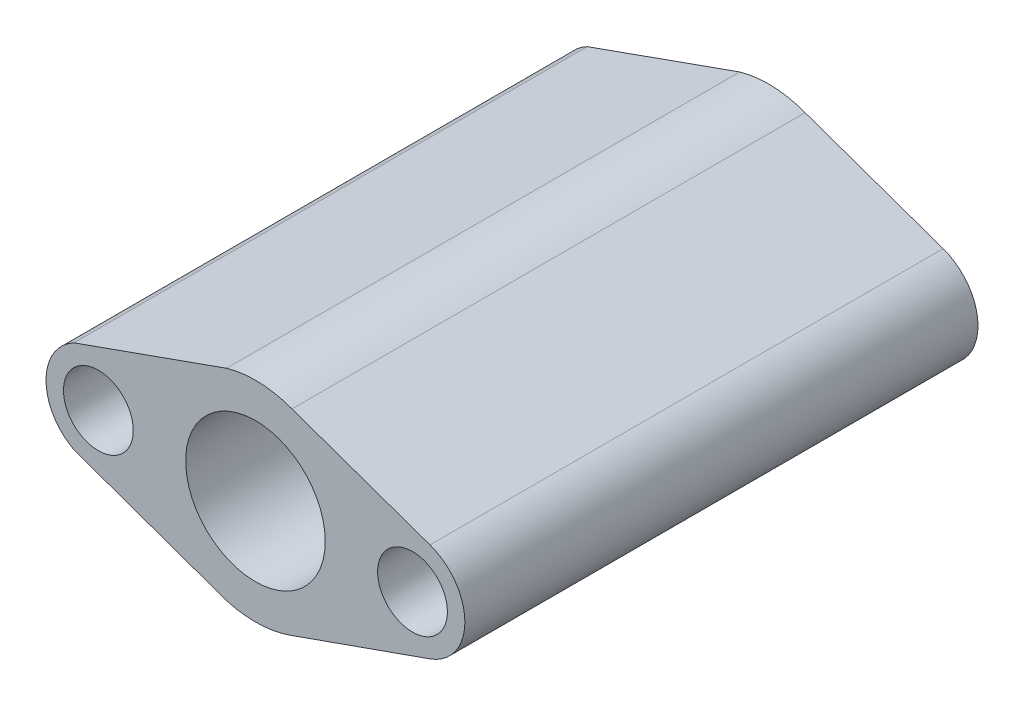
SolidWorks part; units mm, degrees
ref_plane "Front Plane" through (0, 0, 0) normal (0, 0, 1) x (1, 0, 0)
ref_plane "Top Plane" through (0, 0, 0) normal (0, 1, 0) x (1, 0, 0)
ref_plane "Right Plane" through (0, 0, 0) normal (1, 0, 0) x (0, 0, -1)
sketch "Sketch5" plane through (0, 0, 0) normal (0, 0, 1) x (1, 0, 0)
  line L0 (-46.9879, 98.1733) -> (-46.9879, 60.3007) construction
  line L1 (-46.9879, 60.3007) -> (-1.9879, 60.3007) construction
  line L2 (-98.9355, 73.5947) -> (-55.2522, 89.1399)
  line L3 (-36.5084, 88.4108) -> (3.0107, 74.4434)
  line L4 (-36.5084, 32.1906) -> (3.0107, 46.158)
  line L5 (-98.9355, 47.0067) -> (-55.2522, 31.4615)
  circle A0 centre (-46.9879, 60.3007) radius 20
  arc A1 (-58.7999, 32.724) -> (-36.5084, 32.1906) centre (-46.9879, 60.3007) ccw
  arc A2 (3.0107, 46.158) -> (3.0107, 74.4434) centre (-1.9879, 60.3007) ccw
  circle A3 centre (-1.9879, 60.3007) radius 10
  circle A4 centre (-91.9879, 60.3007) radius 10
  arc A5 (-95.0002, 45.6063) -> (-95.0002, 74.9951) centre (-91.9879, 60.3007) cw
  arc A6 (-36.5084, 88.4108) -> (-58.7999, 87.8775) centre (-46.9879, 60.3007) ccw
  dimension "D1" = 40
  dimension "D2" = 60
  dimension "D3" = 20
  dimension "D4" = 30
  dimension "D5" = 90
extrude "Boss-Extrude1" add sketch "Sketch5" against normal blind 147 contours L3 A6 L2 A5 L5 A1 L4 A2 A4 A3 A0
